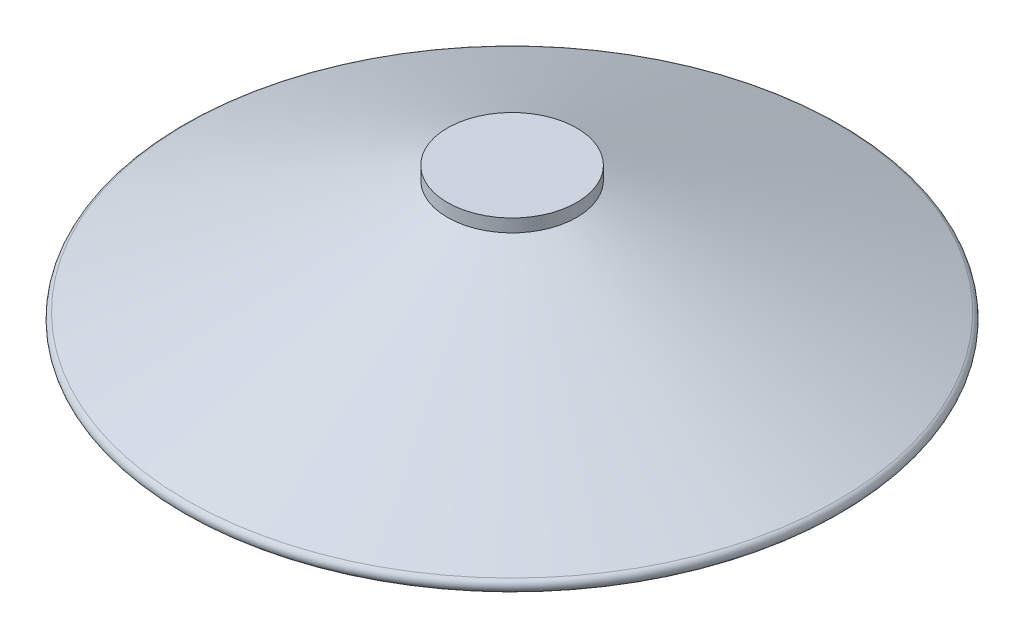
SolidWorks part; units mm, degrees
ref_plane "Front Plane" through (0, 0, 0) normal (0, 0, 1) x (1, 0, 0)
ref_plane "Top Plane" through (0, 0, 0) normal (0, 1, 0) x (1, 0, 0)
ref_plane "Right Plane" through (0, 0, 0) normal (1, 0, 0) x (0, 0, -1)
sketch "Sketch1" plane through (0, 0, 0) normal (0, 0, 1) x (1, 0, 0)
  line L0 (0, 17.7202) -> (0, -7.3937) construction
  line L1 (0, 10.8) -> (-5, 10.8)
  line L2 (-5, 10.8) -> (-5, 9.8)
  line L3 (-5, 9.8) -> (-25.2005, 0.958)
  line L4 (-25, 0) -> (0, 0)
  line L5 (0, 10.8) -> (0, 0)
  arc A0 (-25.2005, 0.958) -> (-25, 0) centre (-25, 0.5) ccw
  dimension "D1" = 0.5
  dimension "D2" = 50
  dimension "D3" = 10
  dimension "D4" = 1
  dimension "D5" = 10.8
revolve "Revolve1" add sketch "Sketch1" angle 360 about L0
sketch "Sketch2" plane through (0, 0, 0) normal (0, 0, 1) x (1, 0, 0)
  line L0 (0, 17.611) -> (0, -10.035) construction
